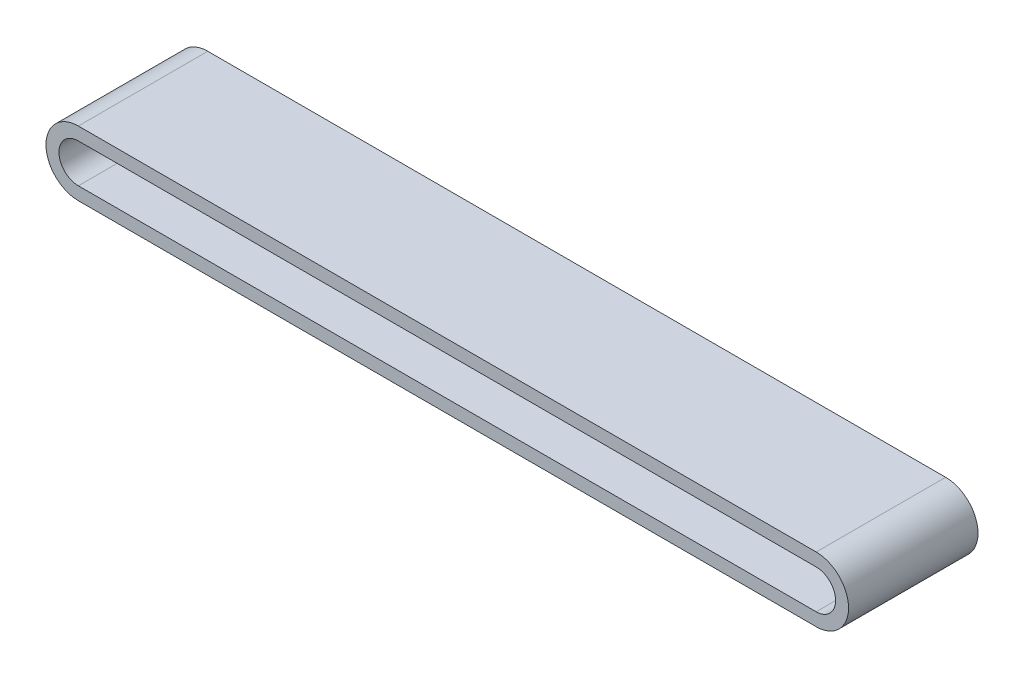
SolidWorks part; units mm, degrees
ref_plane "Front Plane" through (0, 0, 0) normal (0, 0, 1) x (1, 0, 0)
ref_plane "Top Plane" through (0, 0, 0) normal (0, 1, 0) x (1, 0, 0)
ref_plane "Right Plane" through (0, 0, 0) normal (1, 0, 0) x (0, 0, -1)
sketch "Sketch1" plane through (0, 0, 0) normal (0, 0, 1) x (1, 0, 0)
  line L0 (-305.102, 0) -> (264.898, 0) construction
  line L1 (-305.102, 15) -> (264.898, 15)
  line L2 (-305.102, -15) -> (264.898, -15)
  arc A0 (-305.102, 15) -> (-305.102, -15) centre (-305.102, 0) ccw
  arc A1 (264.898, -15) -> (264.898, 15) centre (264.898, 0) ccw
  point P3 (-20.102, 0)
  dimension "D1" = 570
  dimension "D2" = 30
extrude "Extrude-Thin1" add sketch "Sketch1" along normal blind 100 from offset 10 thin contours L1 A1 L2 A0 thin type one direction wall 10
